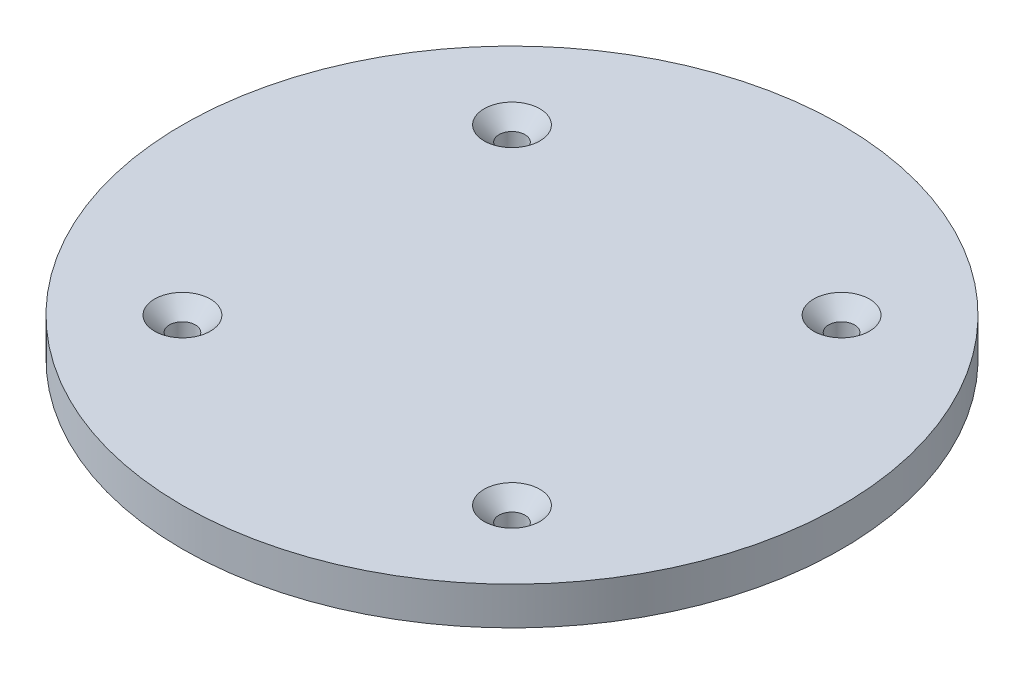
SolidWorks part; units mm, degrees
material "AISI 304"
ref_plane "Front Plane" through (0, 0, 0) normal (0, 0, 1) x (1, 0, 0)
ref_plane "Top Plane" through (0, 0, 0) normal (0, 1, 0) x (1, 0, 0)
ref_plane "Right Plane" through (0, 0, 0) normal (1, 0, 0) x (0, 0, -1)
sketch "Sketch1" plane through (0, 0, 0) normal (0, 1, 0) x (1, 0, 0)
  line L0 (0, 0) -> (0, 25.4) construction
  line L1 (0, 25.4) -> (-25.4, 25.4) construction
  line L3 (-25.4, 25.4) -> (25.4, 25.4)
  line L4 (-25.4, 25.4) -> (-25.4, -25.4)
  line L5 (-25.4, -25.4) -> (25.4, -25.4)
  line L6 (25.4, 25.4) -> (25.4, -25.4)
  circle A0 centre (0, 0) radius 50.8
  circle A1 centre (-25.4, 25.4) radius 2
  circle A2 centre (25.4, 25.4) radius 2
  circle A3 centre (25.4, -25.4) radius 2
  circle A4 centre (-25.4, -25.4) radius 2
  point P13 (0, 0)
  point P14 (-25.4, -26.6095)
  dimension "D1" = 25.4
  dimension "D5" = 101.6
  dimension "D6" = 4
  dimension "D7" = 4
  dimension "D8" = 4
  dimension "D9" = 4
  dimension "D2" = 25.4
  dimension "D3" = 25.4
  dimension "D4" = 50.8
extrude "Boss-Extrude1" add sketch "Sketch1" along normal blind 5.842 contours A0 A4 L4 A1 L3 A2 L6 A3 L5 | A4 L5 A3 L6 A2 L3 A1 L4
chamfer "Chamfer1" distance 2.3 angle 45 4 edges at (25.4, 5.842, 27.4) (25.4, 5.842, -23.4) (-25.4, 5.842, -23.4) (-25.4, 5.842, 27.4)
